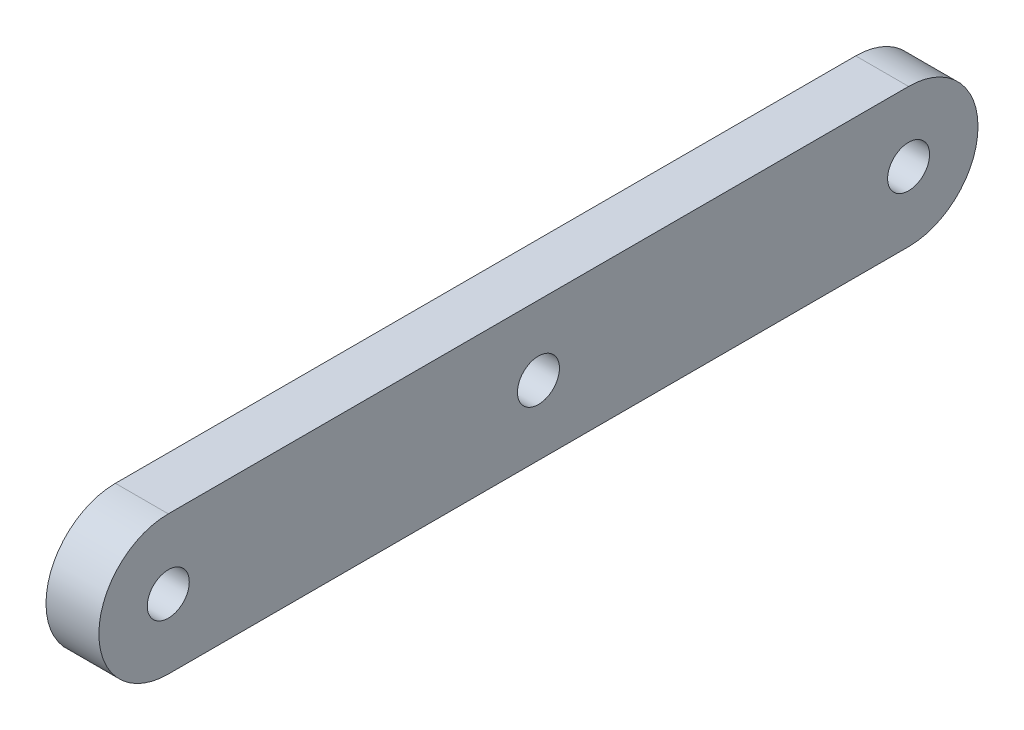
SolidWorks part; units mm, degrees
material "PE High Density"
ref_plane "Front Plane" through (0, 0, 0) normal (0, 0, 1) x (1, 0, 0)
ref_plane "Top Plane" through (0, 0, 0) normal (0, 1, 0) x (1, 0, 0)
ref_plane "Right Plane" through (0, 0, 0) normal (1, 0, 0) x (0, 0, -1)
sketch "Sketch1" plane through (0, 0, 0) normal (1, 0, 0) x (0, 0, -1)
  line L0 (-88.9, 0) -> (0, 0) construction
  line L1 (0, 0) -> (88.9, 0) construction
  line L2 (-88.9, 16.6687) -> (88.9, 16.6687)
  line L3 (88.9, 16.6687) -> (88.9, -16.6687)
  line L4 (88.9, -16.6687) -> (-88.9, -16.6687)
  circle A0 centre (-88.9, 0) radius 16.6687
  circle A1 centre (88.9, 0) radius 16.6687
  dimension "D1" = 88.9
  dimension "D2" = 33.3375
extrude "Boss-Extrude1" add sketch "Sketch1" along normal blind 12.7 contours A0 | A1 L2 A0 L4 | L3 A1 | L3 A1
hole_wizard "3/8 Clearance Hole1" positions "Sketch3" profile "Sketch2" hole size "3/8" standard "ANSI Inch"
sketch "Sketch3" plane through (12.7, 0, 0) normal (1, 0, 0) x (0, 0, -1)
  point P0 (0, 0)
  point P3 (88.9, 0)
  point P6 (-88.9, 0)
sketch "Sketch2" plane through (12.7, 0, 0) normal (0, 1, 0) x (0, 0, -1)
  line L0 (0, 0) -> (0, 15.7295)
  line L1 (0, 15.7295) -> (5.0419, 12.7)
  line L2 (5.0419, 12.7) -> (5.0419, 0)
  line L5 (5.0419, 0) -> (0, 0)
  line L10 (0, 15.7295) -> (-5.0419, 12.7) construction
  line L11 (0, -6.35) -> (0, 107.95) construction
  dimension "Hole Dia." = 10.0838
  dimension "Hole Depth" = 12.7
  dimension "Drill Angle" = 118
